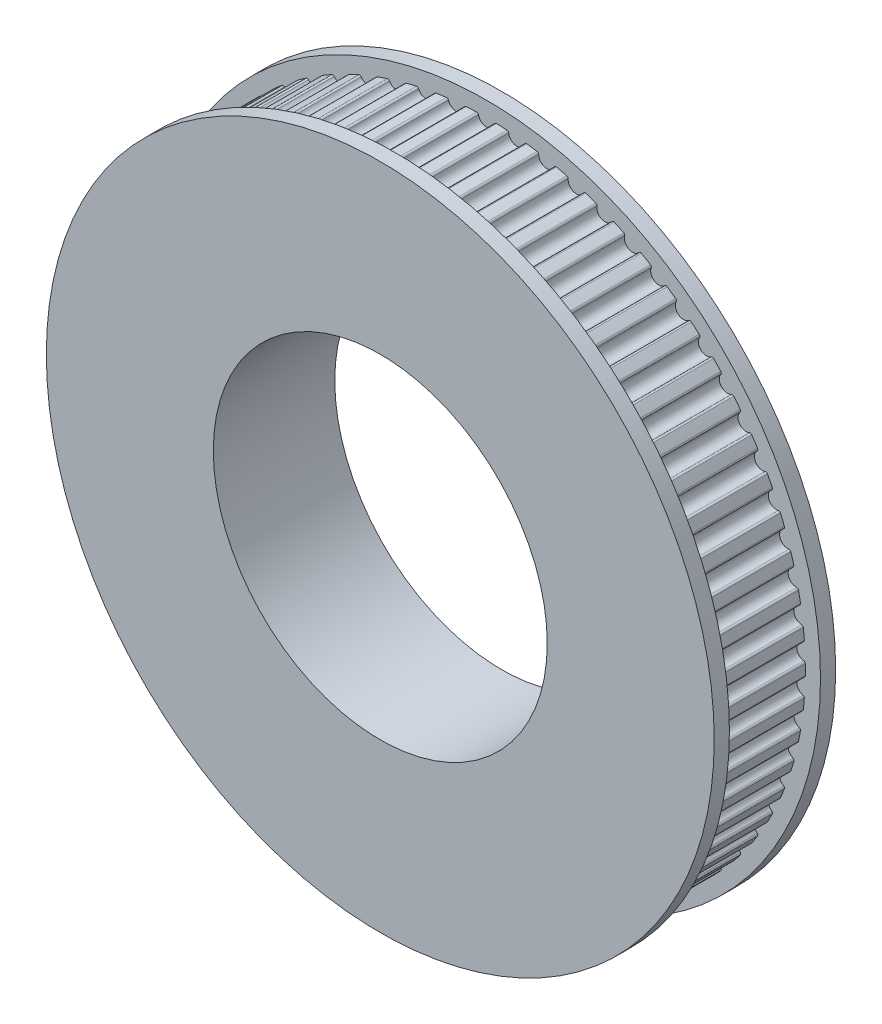
SolidWorks part; units mm, degrees
material "Plain Carbon Steel"
ref_plane "Front Plane" through (0, 0, 0) normal (0, 0, 1) x (1, 0, 0)
ref_plane "Top Plane" through (0, 0, 0) normal (0, 1, 0) x (1, 0, 0)
ref_plane "Right Plane" through (0, 0, 0) normal (1, 0, 0) x (0, 0, -1)
sketch "Sketch1" plane through (0, 0, 0) normal (0, 0, 1) x (1, 0, 0)
  circle A0 centre (0, 0) radius 11
  arc A1 (-0.655, 20.9898) -> (0.655, 20.9898) centre (0, 0) ccw
  arc A2 (-0.5287, 20.8902) -> (0.5287, 20.8902) centre (0, 21) ccw
  arc A3 (0.5287, 20.8902) -> (0.655, 20.9898) centre (0.6511, 20.8648) cw
  arc A4 (-0.5287, 20.8902) -> (-0.655, 20.9898) centre (-0.6511, 20.8648) ccw
  arc A5 (1.3432, 20.957) -> (2.6473, 20.8325) centre (0, 0) ccw
  arc A6 (1.4594, 20.8459) -> (1.3432, 20.957) centre (1.3352, 20.8323) ccw
  arc A7 (1.4594, 20.8459) -> (2.5121, 20.7454) centre (1.9962, 20.9049) ccw
  arc A8 (2.5121, 20.7454) -> (2.6473, 20.8325) centre (2.6315, 20.7085) cw
  arc A9 (3.3292, 20.7344) -> (4.6155, 20.4865) centre (0, 0) ccw
  arc A10 (3.4343, 20.6128) -> (3.3292, 20.7344) centre (3.3093, 20.611) ccw
  arc A11 (3.4343, 20.6128) -> (4.4727, 20.4127) centre (3.9743, 20.6205) ccw
  arc A12 (4.4727, 20.4127) -> (4.6155, 20.4865) centre (4.5881, 20.3646) cw
  arc A13 (5.285, 20.3241) -> (6.542, 19.955) centre (0, 0) ccw
  arc A14 (5.3782, 20.193) -> (5.285, 20.3241) centre (5.2536, 20.2031) ccw
  arc A15 (5.3782, 20.193) -> (6.3928, 19.8951) centre (5.9164, 20.1494) ccw
  arc A16 (6.3928, 19.8951) -> (6.542, 19.955) centre (6.5031, 19.8362) cw
  arc A17 (7.193, 19.7297) -> (8.4092, 19.2428) centre (0, 0) ccw
  arc A18 (7.2733, 19.5903) -> (7.193, 19.7297) centre (7.1502, 19.6122) ccw
  arc A19 (7.2733, 19.5903) -> (8.255, 19.1973) centre (7.8049, 19.4957) ccw
  arc A20 (8.255, 19.1973) -> (8.4092, 19.2428) centre (8.3592, 19.1283) cw
  arc A21 (9.0359, 18.9566) -> (10.2003, 18.3563) centre (0, 0) ccw
  arc A22 (9.1025, 18.8103) -> (9.0359, 18.9566) centre (8.9821, 18.8438) ccw
  arc A23 (9.1025, 18.8103) -> (10.0424, 18.3257) centre (9.6228, 18.6655) ccw
  arc A24 (10.0424, 18.3257) -> (10.2003, 18.3563) centre (10.1396, 18.2471) cw
  arc A25 (10.7969, 18.0119) -> (11.899, 17.3036) centre (0, 0) ccw
  arc A26 (10.8493, 17.8598) -> (10.7969, 18.0119) centre (10.7326, 17.9046) ccw
  arc A27 (10.8493, 17.8598) -> (11.7389, 17.2881) centre (11.3535, 17.6663) ccw
  arc A28 (11.7389, 17.2881) -> (11.899, 17.3036) centre (11.8281, 17.2006) cw
  arc A29 (12.4601, 16.904) -> (13.4899, 16.0942) centre (0, 0) ccw
  arc A30 (12.4979, 16.7477) -> (12.4601, 16.904) centre (12.386, 16.8034) ccw
  arc A31 (12.4979, 16.7477) -> (13.3291, 16.094) centre (12.9813, 16.5071) ccw
  arc A32 (13.3291, 16.094) -> (13.4899, 16.0942) centre (13.4096, 15.9984) cw
  arc A33 (14.0105, 15.643) -> (14.9587, 14.739) centre (0, 0) ccw
  arc A34 (14.0333, 15.4838) -> (14.0105, 15.643) centre (13.9272, 15.5499) ccw
  arc A35 (14.0333, 15.4838) -> (14.7986, 14.7541) centre (14.4917, 15.1984) ccw
  arc A36 (14.7986, 14.7541) -> (14.9587, 14.739) centre (14.8696, 14.6513) cw
  arc A37 (15.4341, 14.2404) -> (16.292, 13.2504) centre (0, 0) ccw
  arc A38 (15.4416, 14.0798) -> (15.4341, 14.2404) centre (15.3422, 14.1557) ccw
  arc A39 (15.4416, 14.0798) -> (16.134, 13.2806) centre (15.8707, 13.7521) ccw
  arc A40 (16.134, 13.2806) -> (16.292, 13.2504) centre (16.195, 13.1715) cw
  arc A41 (16.7178, 12.7088) -> (17.4777, 11.6417) centre (0, 0) ccw
  arc A42 (16.71, 12.5482) -> (16.7178, 12.7088) centre (16.6183, 12.6332) ccw
  arc A43 (16.71, 12.5482) -> (17.3234, 11.6868) centre (17.1061, 12.1812) ccw
  arc A44 (17.3234, 11.6868) -> (17.4777, 11.6417) centre (17.3737, 11.5724) cw
  arc A45 (17.8502, 11.0622) -> (18.5052, 9.9276) centre (0, 0) ccw
  arc A46 (17.8271, 10.903) -> (17.8502, 11.0622) centre (17.7439, 10.9963) ccw
  arc A47 (17.8271, 10.903) -> (18.3559, 9.9872) centre (18.1865, 10.5) ccw
  arc A48 (18.3559, 9.9872) -> (18.5052, 9.9276) centre (18.395, 9.8685) cw
  arc A49 (18.8209, 9.3153) -> (19.3651, 8.1236) centre (0, 0) ccw
  arc A50 (18.7828, 9.1591) -> (18.8209, 9.3153) centre (18.7088, 9.2598) ccw
  arc A51 (18.7828, 9.1591) -> (19.2221, 8.1972) centre (19.1023, 8.7237) ccw
  arc A52 (19.2221, 8.1972) -> (19.3651, 8.1236) centre (19.2498, 8.0753) cw
  arc A53 (19.6211, 7.4841) -> (20.0496, 6.2461) centre (0, 0) ccw
  arc A54 (19.5684, 7.3322) -> (19.6211, 7.4841) centre (19.5043, 7.4395) ccw
  arc A55 (19.5684, 7.3322) -> (19.9142, 6.3329) centre (19.845, 6.8684) ccw
  arc A56 (19.9142, 6.3329) -> (20.0496, 6.2461) centre (19.9303, 6.2089) cw
  arc A57 (20.2437, 5.5851) -> (20.5525, 4.312) centre (0, 0) ccw
  arc A58 (20.1767, 5.4389) -> (20.2437, 5.5851) centre (20.1232, 5.5518) ccw
  arc A59 (20.1767, 5.4389) -> (20.426, 4.4112) centre (20.408, 4.9509) ccw
  arc A60 (20.426, 4.4112) -> (20.5525, 4.312) centre (20.4302, 4.2863) cw
  arc A61 (20.6829, 3.6355) -> (20.8694, 2.3388) centre (0, 0) ccw
  arc A62 (20.6024, 3.4963) -> (20.6829, 3.6355) centre (20.5598, 3.6139) ccw
  arc A63 (20.6024, 3.4963) -> (20.7529, 2.4496) centre (20.7863, 2.9886) ccw
  arc A64 (20.7529, 2.4496) -> (20.8694, 2.3388) centre (20.7451, 2.3249) cw
  arc A65 (20.9348, 1.653) -> (20.9972, 0.3445) centre (0, 0) ccw
  arc A66 (20.8414, 1.5221) -> (20.9348, 1.653) centre (20.8102, 1.6432) ccw
  arc A67 (20.8414, 1.5221) -> (20.8917, 0.4659) centre (20.9762, 0.9992) ccw
  arc A68 (20.8917, 0.4659) -> (20.9972, 0.3445) centre (20.8722, 0.3424) cw
  arc A69 (20.9972, -0.3445) -> (20.9348, -1.653) centre (0, 0) ccw
  arc A70 (20.8917, -0.4659) -> (20.9972, -0.3445) centre (20.8722, -0.3424) ccw
  arc A71 (20.8917, -0.4659) -> (20.8414, -1.5221) centre (20.9762, -0.9992) ccw
  arc A72 (20.8414, -1.5221) -> (20.9348, -1.653) centre (20.8102, -1.6432) cw
  arc A73 (20.8694, -2.3388) -> (20.6829, -3.6355) centre (0, 0) ccw
  arc A74 (20.7529, -2.4496) -> (20.8694, -2.3388) centre (20.7451, -2.3249) ccw
  arc A75 (20.7529, -2.4496) -> (20.6024, -3.4963) centre (20.7863, -2.9886) ccw
  arc A76 (20.6024, -3.4963) -> (20.6829, -3.6355) centre (20.5598, -3.6139) cw
  arc A77 (20.5525, -4.312) -> (20.2437, -5.5851) centre (0, 0) ccw
  arc A78 (20.426, -4.4112) -> (20.5525, -4.312) centre (20.4302, -4.2863) ccw
  arc A79 (20.426, -4.4112) -> (20.1767, -5.4389) centre (20.408, -4.9509) ccw
  arc A80 (20.1767, -5.4389) -> (20.2437, -5.5851) centre (20.1232, -5.5518) cw
  arc A81 (20.0496, -6.2461) -> (19.6211, -7.4841) centre (0, 0) ccw
  arc A82 (19.9142, -6.3329) -> (20.0496, -6.2461) centre (19.9303, -6.2089) ccw
  arc A83 (19.9142, -6.3329) -> (19.5684, -7.3322) centre (19.845, -6.8684) ccw
  arc A84 (19.5684, -7.3322) -> (19.6211, -7.4841) centre (19.5043, -7.4395) cw
  arc A85 (19.3651, -8.1236) -> (18.8209, -9.3153) centre (0, 0) ccw
  arc A86 (19.2221, -8.1972) -> (19.3651, -8.1236) centre (19.2498, -8.0753) ccw
  arc A87 (19.2221, -8.1972) -> (18.7828, -9.1591) centre (19.1023, -8.7237) ccw
  arc A88 (18.7828, -9.1591) -> (18.8209, -9.3153) centre (18.7088, -9.2598) cw
  arc A89 (18.5052, -9.9276) -> (17.8502, -11.0622) centre (0, 0) ccw
  arc A90 (18.3559, -9.9872) -> (18.5052, -9.9276) centre (18.395, -9.8685) ccw
  arc A91 (18.3559, -9.9872) -> (17.8271, -10.903) centre (18.1865, -10.5) ccw
  arc A92 (17.8271, -10.903) -> (17.8502, -11.0622) centre (17.7439, -10.9963) cw
  arc A93 (17.4777, -11.6417) -> (16.7178, -12.7088) centre (0, 0) ccw
  arc A94 (17.3234, -11.6868) -> (17.4777, -11.6417) centre (17.3737, -11.5724) ccw
  arc A95 (17.3234, -11.6868) -> (16.71, -12.5482) centre (17.1061, -12.1812) ccw
  arc A96 (16.71, -12.5482) -> (16.7178, -12.7088) centre (16.6183, -12.6332) cw
  arc A97 (16.292, -13.2504) -> (15.4341, -14.2404) centre (0, 0) ccw
  arc A98 (16.134, -13.2806) -> (16.292, -13.2504) centre (16.195, -13.1715) ccw
  arc A99 (16.134, -13.2806) -> (15.4416, -14.0798) centre (15.8707, -13.7521) ccw
  arc A100 (15.4416, -14.0798) -> (15.4341, -14.2404) centre (15.3422, -14.1557) cw
  arc A101 (14.9587, -14.739) -> (14.0105, -15.643) centre (0, 0) ccw
  arc A102 (14.7986, -14.7541) -> (14.9587, -14.739) centre (14.8696, -14.6513) ccw
  arc A103 (14.7986, -14.7541) -> (14.0333, -15.4838) centre (14.4917, -15.1984) ccw
  arc A104 (14.0333, -15.4838) -> (14.0105, -15.643) centre (13.9272, -15.5499) cw
  arc A105 (13.4899, -16.0942) -> (12.4601, -16.904) centre (0, 0) ccw
  arc A106 (13.3291, -16.094) -> (13.4899, -16.0942) centre (13.4096, -15.9984) ccw
  arc A107 (13.3291, -16.094) -> (12.4979, -16.7477) centre (12.9813, -16.5071) ccw
  arc A108 (12.4979, -16.7477) -> (12.4601, -16.904) centre (12.386, -16.8034) cw
  arc A109 (11.899, -17.3036) -> (10.7969, -18.0119) centre (0, 0) ccw
  arc A110 (11.7389, -17.2881) -> (11.899, -17.3036) centre (11.8281, -17.2006) ccw
  arc A111 (11.7389, -17.2881) -> (10.8493, -17.8598) centre (11.3535, -17.6663) ccw
  arc A112 (10.8493, -17.8598) -> (10.7969, -18.0119) centre (10.7326, -17.9046) cw
  arc A113 (10.2003, -18.3563) -> (9.0359, -18.9566) centre (0, 0) ccw
  arc A114 (10.0424, -18.3257) -> (10.2003, -18.3563) centre (10.1396, -18.2471) ccw
  arc A115 (10.0424, -18.3257) -> (9.1025, -18.8103) centre (9.6228, -18.6655) ccw
  arc A116 (9.1025, -18.8103) -> (9.0359, -18.9566) centre (8.9821, -18.8438) cw
  arc A117 (8.4092, -19.2428) -> (7.193, -19.7297) centre (0, 0) ccw
  arc A118 (8.255, -19.1973) -> (8.4092, -19.2428) centre (8.3592, -19.1283) ccw
  arc A119 (8.255, -19.1973) -> (7.2733, -19.5903) centre (7.8049, -19.4957) ccw
  arc A120 (7.2733, -19.5903) -> (7.193, -19.7297) centre (7.1502, -19.6122) cw
  arc A121 (6.542, -19.955) -> (5.285, -20.3241) centre (0, 0) ccw
  arc A122 (6.3928, -19.8951) -> (6.542, -19.955) centre (6.5031, -19.8362) ccw
  arc A123 (6.3928, -19.8951) -> (5.3782, -20.193) centre (5.9164, -20.1494) ccw
  arc A124 (5.3782, -20.193) -> (5.285, -20.3241) centre (5.2536, -20.2031) cw
  arc A125 (4.6155, -20.4865) -> (3.3292, -20.7344) centre (0, 0) ccw
  arc A126 (4.4727, -20.4127) -> (4.6155, -20.4865) centre (4.5881, -20.3646) ccw
  arc A127 (4.4727, -20.4127) -> (3.4343, -20.6128) centre (3.9743, -20.6205) ccw
  arc A128 (3.4343, -20.6128) -> (3.3292, -20.7344) centre (3.3093, -20.611) cw
  arc A129 (2.6473, -20.8325) -> (1.3432, -20.957) centre (0, 0) ccw
  arc A130 (2.5121, -20.7454) -> (2.6473, -20.8325) centre (2.6315, -20.7085) ccw
  arc A131 (2.5121, -20.7454) -> (1.4594, -20.8459) centre (1.9962, -20.9049) ccw
  arc A132 (1.4594, -20.8459) -> (1.3432, -20.957) centre (1.3352, -20.8323) cw
  arc A133 (0.655, -20.9898) -> (-0.655, -20.9898) centre (0, 0) ccw
  arc A134 (0.5287, -20.8902) -> (0.655, -20.9898) centre (0.6511, -20.8648) ccw
  arc A135 (0.5287, -20.8902) -> (-0.5287, -20.8902) centre (0, -21) ccw
  arc A136 (-0.5287, -20.8902) -> (-0.655, -20.9898) centre (-0.6511, -20.8648) cw
  arc A137 (-1.3432, -20.957) -> (-2.6473, -20.8325) centre (0, 0) ccw
  arc A138 (-1.4594, -20.8459) -> (-1.3432, -20.957) centre (-1.3352, -20.8323) ccw
  arc A139 (-1.4594, -20.8459) -> (-2.5121, -20.7454) centre (-1.9962, -20.9049) ccw
  arc A140 (-2.5121, -20.7454) -> (-2.6473, -20.8325) centre (-2.6315, -20.7085) cw
  arc A141 (-3.3292, -20.7344) -> (-4.6155, -20.4865) centre (0, 0) ccw
  arc A142 (-3.4343, -20.6128) -> (-3.3292, -20.7344) centre (-3.3093, -20.611) ccw
  arc A143 (-3.4343, -20.6128) -> (-4.4727, -20.4127) centre (-3.9743, -20.6205) ccw
  arc A144 (-4.4727, -20.4127) -> (-4.6155, -20.4865) centre (-4.5881, -20.3646) cw
  arc A145 (-5.285, -20.3241) -> (-6.542, -19.955) centre (0, 0) ccw
  arc A146 (-5.3782, -20.193) -> (-5.285, -20.3241) centre (-5.2536, -20.2031) ccw
  arc A147 (-5.3782, -20.193) -> (-6.3928, -19.8951) centre (-5.9164, -20.1494) ccw
  arc A148 (-6.3928, -19.8951) -> (-6.542, -19.955) centre (-6.5031, -19.8362) cw
  arc A149 (-7.193, -19.7297) -> (-8.4092, -19.2428) centre (0, 0) ccw
  arc A150 (-7.2733, -19.5903) -> (-7.193, -19.7297) centre (-7.1502, -19.6122) ccw
  arc A151 (-7.2733, -19.5903) -> (-8.255, -19.1973) centre (-7.8049, -19.4957) ccw
  arc A152 (-8.255, -19.1973) -> (-8.4092, -19.2428) centre (-8.3592, -19.1283) cw
  arc A153 (-9.0359, -18.9566) -> (-10.2003, -18.3563) centre (0, 0) ccw
  arc A154 (-9.1025, -18.8103) -> (-9.0359, -18.9566) centre (-8.9821, -18.8438) ccw
  arc A155 (-9.1025, -18.8103) -> (-10.0424, -18.3257) centre (-9.6228, -18.6655) ccw
  arc A156 (-10.0424, -18.3257) -> (-10.2003, -18.3563) centre (-10.1396, -18.2471) cw
  arc A157 (-10.7969, -18.0119) -> (-11.899, -17.3036) centre (0, 0) ccw
  arc A158 (-10.8493, -17.8598) -> (-10.7969, -18.0119) centre (-10.7326, -17.9046) ccw
  arc A159 (-10.8493, -17.8598) -> (-11.7389, -17.2881) centre (-11.3535, -17.6663) ccw
  arc A160 (-11.7389, -17.2881) -> (-11.899, -17.3036) centre (-11.8281, -17.2006) cw
  arc A161 (-12.4601, -16.904) -> (-13.4899, -16.0942) centre (0, 0) ccw
  arc A162 (-12.4979, -16.7477) -> (-12.4601, -16.904) centre (-12.386, -16.8034) ccw
  arc A163 (-12.4979, -16.7477) -> (-13.3291, -16.094) centre (-12.9813, -16.5071) ccw
  arc A164 (-13.3291, -16.094) -> (-13.4899, -16.0942) centre (-13.4096, -15.9984) cw
  arc A165 (-14.0105, -15.643) -> (-14.9587, -14.739) centre (0, 0) ccw
  arc A166 (-14.0333, -15.4838) -> (-14.0105, -15.643) centre (-13.9272, -15.5499) ccw
  arc A167 (-14.0333, -15.4838) -> (-14.7986, -14.7541) centre (-14.4917, -15.1984) ccw
  arc A168 (-14.7986, -14.7541) -> (-14.9587, -14.739) centre (-14.8696, -14.6513) cw
  arc A169 (-15.4341, -14.2404) -> (-16.292, -13.2504) centre (0, 0) ccw
  arc A170 (-15.4416, -14.0798) -> (-15.4341, -14.2404) centre (-15.3422, -14.1557) ccw
  arc A171 (-15.4416, -14.0798) -> (-16.134, -13.2806) centre (-15.8707, -13.7521) ccw
  arc A172 (-16.134, -13.2806) -> (-16.292, -13.2504) centre (-16.195, -13.1715) cw
  arc A173 (-16.7178, -12.7088) -> (-17.4777, -11.6417) centre (0, 0) ccw
  arc A174 (-16.71, -12.5482) -> (-16.7178, -12.7088) centre (-16.6183, -12.6332) ccw
  arc A175 (-16.71, -12.5482) -> (-17.3234, -11.6868) centre (-17.1061, -12.1812) ccw
  arc A176 (-17.3234, -11.6868) -> (-17.4777, -11.6417) centre (-17.3737, -11.5724) cw
  arc A177 (-17.8502, -11.0622) -> (-18.5052, -9.9276) centre (0, 0) ccw
  arc A178 (-17.8271, -10.903) -> (-17.8502, -11.0622) centre (-17.7439, -10.9963) ccw
  arc A179 (-17.8271, -10.903) -> (-18.3559, -9.9872) centre (-18.1865, -10.5) ccw
  arc A180 (-18.3559, -9.9872) -> (-18.5052, -9.9276) centre (-18.395, -9.8685) cw
  arc A181 (-18.8209, -9.3153) -> (-19.3651, -8.1236) centre (0, 0) ccw
  arc A182 (-18.7828, -9.1591) -> (-18.8209, -9.3153) centre (-18.7088, -9.2598) ccw
  arc A183 (-18.7828, -9.1591) -> (-19.2221, -8.1972) centre (-19.1023, -8.7237) ccw
  arc A184 (-19.2221, -8.1972) -> (-19.3651, -8.1236) centre (-19.2498, -8.0753) cw
  arc A185 (-19.6211, -7.4841) -> (-20.0496, -6.2461) centre (0, 0) ccw
  arc A186 (-19.5684, -7.3322) -> (-19.6211, -7.4841) centre (-19.5043, -7.4395) ccw
  arc A187 (-19.5684, -7.3322) -> (-19.9142, -6.3329) centre (-19.845, -6.8684) ccw
  arc A188 (-19.9142, -6.3329) -> (-20.0496, -6.2461) centre (-19.9303, -6.2089) cw
  arc A189 (-20.2437, -5.5851) -> (-20.5525, -4.312) centre (0, 0) ccw
  arc A190 (-20.1767, -5.4389) -> (-20.2437, -5.5851) centre (-20.1232, -5.5518) ccw
  arc A191 (-20.1767, -5.4389) -> (-20.426, -4.4112) centre (-20.408, -4.9509) ccw
  arc A192 (-20.426, -4.4112) -> (-20.5525, -4.312) centre (-20.4302, -4.2863) cw
  arc A193 (-20.6829, -3.6355) -> (-20.8694, -2.3388) centre (0, 0) ccw
  arc A194 (-20.6024, -3.4963) -> (-20.6829, -3.6355) centre (-20.5598, -3.6139) ccw
  arc A195 (-20.6024, -3.4963) -> (-20.7529, -2.4496) centre (-20.7863, -2.9886) ccw
  arc A196 (-20.7529, -2.4496) -> (-20.8694, -2.3388) centre (-20.7451, -2.3249) cw
  arc A197 (-20.9348, -1.653) -> (-20.9972, -0.3445) centre (0, 0) ccw
  arc A198 (-20.8414, -1.5221) -> (-20.9348, -1.653) centre (-20.8102, -1.6432) ccw
  arc A199 (-20.8414, -1.5221) -> (-20.8917, -0.4659) centre (-20.9762, -0.9992) ccw
  arc A200 (-20.8917, -0.4659) -> (-20.9972, -0.3445) centre (-20.8722, -0.3424) cw
  arc A201 (-20.9972, 0.3445) -> (-20.9348, 1.653) centre (0, 0) ccw
  arc A202 (-20.8917, 0.4659) -> (-20.9972, 0.3445) centre (-20.8722, 0.3424) ccw
  arc A203 (-20.8917, 0.4659) -> (-20.8414, 1.5221) centre (-20.9762, 0.9992) ccw
  arc A204 (-20.8414, 1.5221) -> (-20.9348, 1.653) centre (-20.8102, 1.6432) cw
  arc A205 (-20.8694, 2.3388) -> (-20.6829, 3.6355) centre (0, 0) ccw
  arc A206 (-20.7529, 2.4496) -> (-20.8694, 2.3388) centre (-20.7451, 2.3249) ccw
  arc A207 (-20.7529, 2.4496) -> (-20.6024, 3.4963) centre (-20.7863, 2.9886) ccw
  arc A208 (-20.6024, 3.4963) -> (-20.6829, 3.6355) centre (-20.5598, 3.6139) cw
  arc A209 (-20.5525, 4.312) -> (-20.2437, 5.5851) centre (0, 0) ccw
  arc A210 (-20.426, 4.4112) -> (-20.5525, 4.312) centre (-20.4302, 4.2863) ccw
  arc A211 (-20.426, 4.4112) -> (-20.1767, 5.4389) centre (-20.408, 4.9509) ccw
  arc A212 (-20.1767, 5.4389) -> (-20.2437, 5.5851) centre (-20.1232, 5.5518) cw
  arc A213 (-20.0496, 6.2461) -> (-19.6211, 7.4841) centre (0, 0) ccw
  arc A214 (-19.9142, 6.3329) -> (-20.0496, 6.2461) centre (-19.9303, 6.2089) ccw
  arc A215 (-19.9142, 6.3329) -> (-19.5684, 7.3322) centre (-19.845, 6.8684) ccw
  arc A216 (-19.5684, 7.3322) -> (-19.6211, 7.4841) centre (-19.5043, 7.4395) cw
  arc A217 (-19.3651, 8.1236) -> (-18.8209, 9.3153) centre (0, 0) ccw
  arc A218 (-19.2221, 8.1972) -> (-19.3651, 8.1236) centre (-19.2498, 8.0753) ccw
  arc A219 (-19.2221, 8.1972) -> (-18.7828, 9.1591) centre (-19.1023, 8.7237) ccw
  arc A220 (-18.7828, 9.1591) -> (-18.8209, 9.3153) centre (-18.7088, 9.2598) cw
  arc A221 (-18.5052, 9.9276) -> (-17.8502, 11.0622) centre (0, 0) ccw
  arc A222 (-18.3559, 9.9872) -> (-18.5052, 9.9276) centre (-18.395, 9.8685) ccw
  arc A223 (-18.3559, 9.9872) -> (-17.8271, 10.903) centre (-18.1865, 10.5) ccw
  arc A224 (-17.8271, 10.903) -> (-17.8502, 11.0622) centre (-17.7439, 10.9963) cw
  arc A225 (-17.4777, 11.6417) -> (-16.7178, 12.7088) centre (0, 0) ccw
  arc A226 (-17.3234, 11.6868) -> (-17.4777, 11.6417) centre (-17.3737, 11.5724) ccw
  arc A227 (-17.3234, 11.6868) -> (-16.71, 12.5482) centre (-17.1061, 12.1812) ccw
  arc A228 (-16.71, 12.5482) -> (-16.7178, 12.7088) centre (-16.6183, 12.6332) cw
  arc A229 (-16.292, 13.2504) -> (-15.4341, 14.2404) centre (0, 0) ccw
  arc A230 (-16.134, 13.2806) -> (-16.292, 13.2504) centre (-16.195, 13.1715) ccw
  arc A231 (-16.134, 13.2806) -> (-15.4416, 14.0798) centre (-15.8707, 13.7521) ccw
  arc A232 (-15.4416, 14.0798) -> (-15.4341, 14.2404) centre (-15.3422, 14.1557) cw
  arc A233 (-14.9587, 14.739) -> (-14.0105, 15.643) centre (0, 0) ccw
  arc A234 (-14.7986, 14.7541) -> (-14.9587, 14.739) centre (-14.8696, 14.6513) ccw
  arc A235 (-14.7986, 14.7541) -> (-14.0333, 15.4838) centre (-14.4917, 15.1984) ccw
  arc A236 (-14.0333, 15.4838) -> (-14.0105, 15.643) centre (-13.9272, 15.5499) cw
  arc A237 (-13.4899, 16.0942) -> (-12.4601, 16.904) centre (0, 0) ccw
  arc A238 (-13.3291, 16.094) -> (-13.4899, 16.0942) centre (-13.4096, 15.9984) ccw
  arc A239 (-13.3291, 16.094) -> (-12.4979, 16.7477) centre (-12.9813, 16.5071) ccw
  arc A240 (-12.4979, 16.7477) -> (-12.4601, 16.904) centre (-12.386, 16.8034) cw
  arc A241 (-11.899, 17.3036) -> (-10.7969, 18.0119) centre (0, 0) ccw
  arc A242 (-11.7389, 17.2881) -> (-11.899, 17.3036) centre (-11.8281, 17.2006) ccw
  arc A243 (-11.7389, 17.2881) -> (-10.8493, 17.8598) centre (-11.3535, 17.6663) ccw
  arc A244 (-10.8493, 17.8598) -> (-10.7969, 18.0119) centre (-10.7326, 17.9046) cw
  arc A245 (-10.2003, 18.3563) -> (-9.0359, 18.9566) centre (0, 0) ccw
  arc A246 (-10.0424, 18.3257) -> (-10.2003, 18.3563) centre (-10.1396, 18.2471) ccw
  arc A247 (-10.0424, 18.3257) -> (-9.1025, 18.8103) centre (-9.6228, 18.6655) ccw
  arc A248 (-9.1025, 18.8103) -> (-9.0359, 18.9566) centre (-8.9821, 18.8438) cw
  arc A249 (-8.4092, 19.2428) -> (-7.193, 19.7297) centre (0, 0) ccw
  arc A250 (-8.255, 19.1973) -> (-8.4092, 19.2428) centre (-8.3592, 19.1283) ccw
  arc A251 (-8.255, 19.1973) -> (-7.2733, 19.5903) centre (-7.8049, 19.4957) ccw
  arc A252 (-7.2733, 19.5903) -> (-7.193, 19.7297) centre (-7.1502, 19.6122) cw
  arc A253 (-6.542, 19.955) -> (-5.285, 20.3241) centre (0, 0) ccw
  arc A254 (-6.3928, 19.8951) -> (-6.542, 19.955) centre (-6.5031, 19.8362) ccw
  arc A255 (-6.3928, 19.8951) -> (-5.3782, 20.193) centre (-5.9164, 20.1494) ccw
  arc A256 (-5.3782, 20.193) -> (-5.285, 20.3241) centre (-5.2536, 20.2031) cw
  arc A257 (-4.6155, 20.4865) -> (-3.3292, 20.7344) centre (0, 0) ccw
  arc A258 (-4.4727, 20.4127) -> (-4.6155, 20.4865) centre (-4.5881, 20.3646) ccw
  arc A259 (-4.4727, 20.4127) -> (-3.4343, 20.6128) centre (-3.9743, 20.6205) ccw
  arc A260 (-3.4343, 20.6128) -> (-3.3292, 20.7344) centre (-3.3093, 20.611) cw
  arc A261 (-2.6473, 20.8325) -> (-1.3432, 20.957) centre (0, 0) ccw
  arc A262 (-2.5121, 20.7454) -> (-2.6473, 20.8325) centre (-2.6315, 20.7085) ccw
  arc A263 (-2.5121, 20.7454) -> (-1.4594, 20.8459) centre (-1.9962, 20.9049) ccw
  arc A264 (-1.4594, 20.8459) -> (-1.3432, 20.957) centre (-1.3352, 20.8323) cw
  point P468 (0, 0)
  dimension "D1" = 0.125
extrude "Boss-Extrude1" add sketch "Sketch1" along normal blind 6
sketch "Sketch2" plane through (0, 0, 6) normal (0, 0, 1) x (1, 0, 0)
  circle A0 centre (0, 14) radius 3 construction
  dimension "D1" = 14
sketch "Sketch3" plane through (0, 0, 6) normal (0, 0, 1) x (1, 0, 0)
  circle A0 centre (0, 0) radius 22
  circle A1 centre (0, 0) radius 11
extrude "Boss-Extrude2" add sketch "Sketch3" along normal blind 1
sketch "Sketch4" plane through (0, 0, 0) normal (0, 0, -1) x (-1, 0, 0)
  circle A0 centre (0, 0) radius 22
  circle A1 centre (0, 0) radius 11
extrude "Boss-Extrude3" add sketch "Sketch4" along normal blind 1
